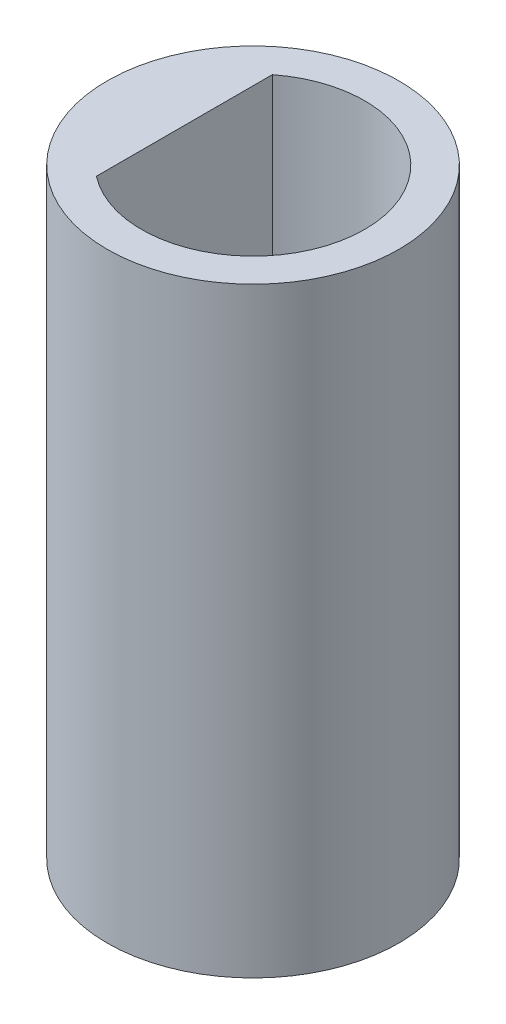
SolidWorks part; units mm, degrees
ref_plane "Alzado" through (0, 0, 0) normal (0, 0, 1) x (1, 0, 0)
ref_plane "Planta" through (0, 0, 0) normal (0, 1, 0) x (1, 0, 0)
ref_plane "Vista lateral" through (0, 0, 0) normal (1, 0, 0) x (0, 0, -1)
sketch "Croquis2" plane through (0, 0, 0) normal (0, 1, 0) x (1, 0, 0)
  circle A0 centre (0, 0) radius 3.4
  dimension "D1" = 6.8
extrude "Saliente-Extruir1" add sketch "Croquis2" along normal blind 14
sketch "Croquis3" plane through (0, 14, 0) normal (0, 1, 0) x (1, 0, 0)
  line L0 (-1.6, 2.0494) -> (-1.6, -2.0494)
  arc A0 (-1.6, -2.0494) -> (-1.6, 2.0494) centre (0, 0) ccw
  dimension "D1" = 5.2
  dimension "D2" = 4.2
extrude "Cortar-Extruir1" cut sketch "Croquis3" against normal through all
